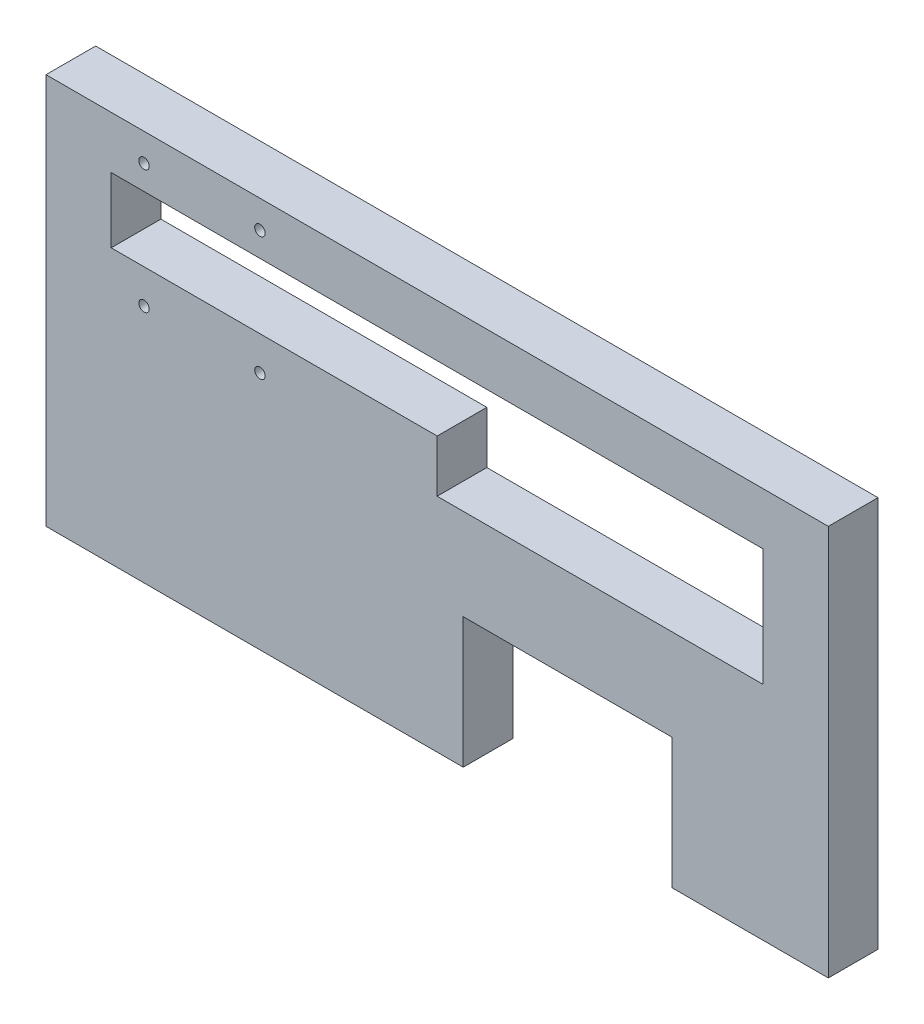
SolidWorks part; units mm, degrees
ref_plane "Front Plane" through (0, 0, 0) normal (0, 0, 1) x (1, 0, 0)
ref_plane "Top Plane" through (0, 0, 0) normal (0, 1, 0) x (1, 0, 0)
ref_plane "Right Plane" through (0, 0, 0) normal (1, 0, 0) x (0, 0, -1)
sketch "Sketch1" plane through (0, 0, 0) normal (0, 0, 1) x (1, 0, 0)
  line L1 (0, 0) -> (300, 0)
  line L2 (0, 0) -> (0, 150)
  line L3 (0, 150) -> (300, 150)
  line L4 (300, 0) -> (300, 150)
  dimension "D1" = 300
  dimension "D2" = 150
extrude "block" add sketch "Sketch1" against normal blind 19.05
sketch "Sketch3" plane through (0, 0, 0) normal (0, 0, 1) x (1, 0, 0)
  line L0 (0, 150) -> (0, 0) construction
  line L1 (25, 130) -> (275, 130)
  line L2 (25, 130) -> (25, 105)
  line L3 (25, 105) -> (275, 105)
  line L4 (275, 130) -> (275, 105)
  line L5 (300, 150) -> (0, 150) construction
  dimension "D1" = 25
  dimension "D2" = 250
  dimension "D3" = 25
  dimension "D4" = 20
extrude "Cut-Extrude2" cut sketch "Sketch3" against normal up to surface (39.9612 mm away)
sketch "Sketch6" plane through (0, 0, 0) normal (0, 0, 1) x (1, 0, 0)
  line L1 (275, 105) -> (150, 105)
  line L2 (275, 105) -> (275, 85)
  line L3 (275, 85) -> (150, 85)
  line L4 (150, 105) -> (150, 85)
  dimension "D1" = 20
  dimension "D2" = 125
extrude "Cut-Extrude5" cut sketch "Sketch6" against normal through all
sketch "Sketch7" plane through (0, 0, 0) normal (0, 0, 1) x (1, 0, 0)
  line L0 (0, 0) -> (300, 0) construction
  line L1 (240, 0) -> (160, 0)
  line L2 (240, 0) -> (240, 50)
  line L3 (240, 50) -> (160, 50)
  line L4 (160, 0) -> (160, 50)
  dimension "D1" = 80
  dimension "D2" = 50
  dimension "D3" = 60
extrude "Cut-Extrude6" cut sketch "Sketch7" against normal through all
sketch "Sketch8" plane through (0, 0, 0) normal (0, 0, 1) x (1, 0, 0)
  circle A0 centre (37.5875, 139.35) radius 2
  circle A1 centre (82.0375, 139.35) radius 2
  circle A2 centre (37.5875, 91.95) radius 2
  circle A3 centre (82.0375, 91.95) radius 2
extrude "Cut-Extrude7" cut sketch "Sketch8" against normal through all
